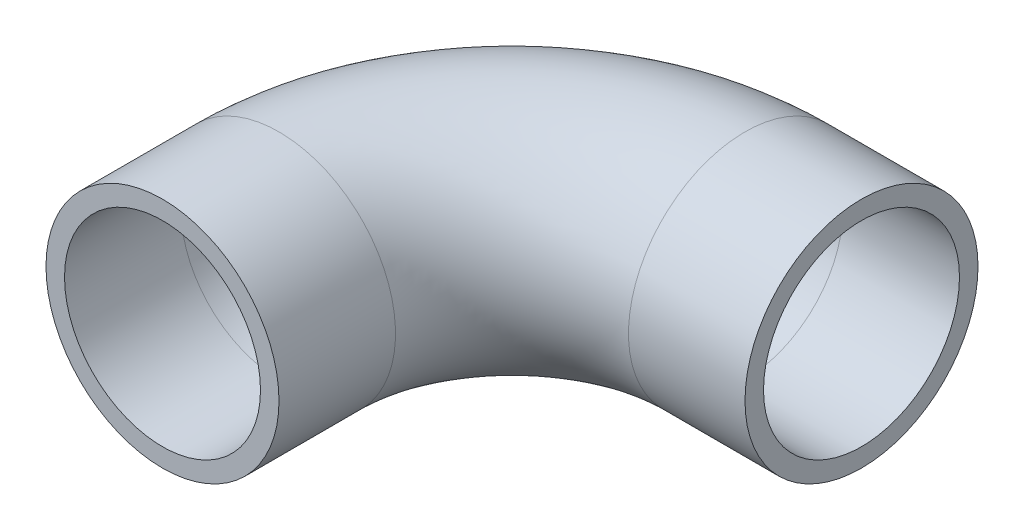
SolidWorks part; units mm, degrees
material "PVC Rigid"
ref_plane "Front Plane" through (0, 0, 0) normal (0, 0, 1) x (1, 0, 0)
ref_plane "Top Plane" through (0, 0, 0) normal (0, 1, 0) x (1, 0, 0)
ref_plane "Right Plane" through (0, 0, 0) normal (1, 0, 0) x (0, 0, -1)
sketch "Sketch1" plane through (0, 0, 0) normal (0, 0, 1) x (1, 0, 0)
  circle A0 centre (0, 0) radius 12.7
  circle A1 centre (0, 0) radius 10.6807
  dimension "D1" = 21.3614
  dimension "D2" = 25.4
sketch "Sketch15" plane through (0, 0, 0) normal (0, 1, 0) x (1, 0, 0)
  line L0 (0, 0) -> (0, 12.7)
  line L1 (25.4, 38.1) -> (38.1, 38.1)
  arc A0 (0, 12.7) -> (25.4, 38.1) centre (25.4, 12.7) cw
  dimension "D2" = 25.4
  dimension "D1" = 12.7
sweep "Sweep7" add profiles "Sketch1" path "Sketch15"
